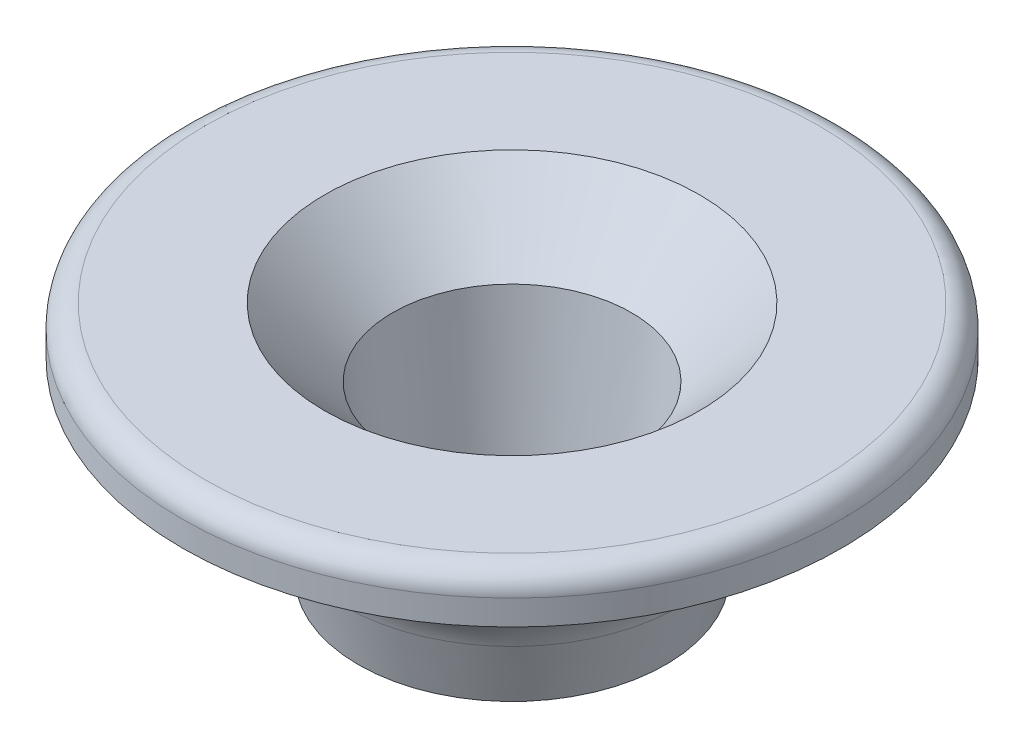
SolidWorks part; units mm, degrees
ref_plane "Plan de face" through (0, 0, 0) normal (0, 0, 1) x (1, 0, 0)
ref_plane "Plan de dessus" through (0, 0, 0) normal (0, 1, 0) x (1, 0, 0)
ref_plane "Plan de droite" through (0, 0, 0) normal (1, 0, 0) x (0, 0, -1)
sketch "Esquisse1" plane through (0, 0, 0) normal (0, 0, 1) x (1, 0, 0)
  line L0 (0, 31.9985) -> (0, -36.8638) construction
  line L1 (-8.23, 14.2884) -> (-14.48, 14.2884)
  line L2 (-14.48, 14.2884) -> (-14.48, 12.1884)
  line L3 (-14.48, 12.1884) -> (-10.48, 12.1884)
  line L4 (-10.48, 12.1884) -> (-10.48, 9.7884)
  line L5 (-4.4, 3.8884) -> (-6.75, 3.8884)
  line L8 (-8.23, 14.2884) -> (-5.25, 11.2884)
  line L9 (-4.4, 3.8884) -> (-5.25, 11.2884)
  line L10 (-10.48, 9.7884) -> (-7.75, 7.8884)
  line L11 (-7.75, 7.8884) -> (-6.75, 3.8884)
  point P5 (0, 7.8884)
  dimension "D1" = 2.35
  dimension "D2" = 2.1
  dimension "D3" = 4
  dimension "D4" = 2.4
  dimension "D5" = 2.98
  dimension "D6" = 7.4
  dimension "D7" = 3.73
  dimension "D8" = 4.4
  dimension "D9" = 6.25
  dimension "D10" = 4
revolve "Révolution1" add sketch "Esquisse1" angle 360 about L0
fillet "Congé1" radius 4 1 edges at (0, 7.8884, 7.75)
fillet "Congé2" radius 0.5 1 edges at (0, 3.8884, 4.4)
fillet "Congé4" radius 1 1 edges at (0, 14.2884, 14.48)
